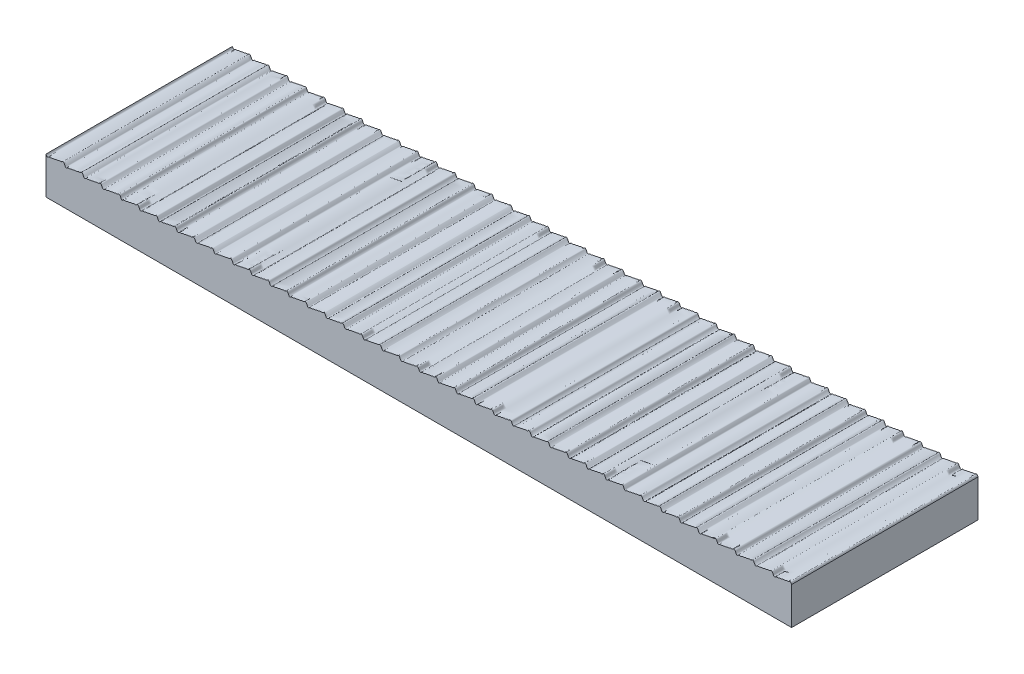
SolidWorks part; units mm, degrees
ref_plane "Ebene vorne" through (0, 0, 0) normal (0, 0, 1) x (1, 0, 0)
ref_plane "Ebene oben" through (0, 0, 0) normal (0, 1, 0) x (1, 0, 0)
ref_plane "Ebene rechts" through (0, 0, 0) normal (1, 0, 0) x (0, 0, -1)
sketch "Skizze1" plane through (0, 0, 0) normal (0, 0, 1) x (1, 0, 0)
  line L0 (0, 10) -> (200, 10) construction
  line L1 (0, 10) -> (0, 0)
  line L2 (0, 0) -> (200, 0)
  line L3 (200, 0) -> (200, 10)
  line L4 (0, 9.5082) -> (200, 9.5082) construction
  line L5 (4.9934, 10) -> (4.9934, 0) construction
  spline S0 degree 4 poles (-19.803, 9.6528) (-19.7633, 9.5821) (-19.6151, 9.4174) (-19.3083, 9.6469) (-18.9908, 9.8083) (-18.4989, 9.6674) (-18.1706, 10.0052) (-17.7456, 9.8267) (-17.4168, 10.0962) (-17.0344, 10.079) (-16.6491, 10.1079) (-16.3335, 10.3555) (-15.9223, 10.188) (-15.6947, 10.3697) (-15.3546, 10.605) (-15.1185, 10.2325) (-14.963, 9.9948) (-14.8192, 9.5069) (-14.4461, 9.4519) (-14.2053, 9.7572) (-13.9579, 9.7444) (-13.656, 9.695) (-13.3717, 9.8513) (-13.0365, 9.9455) (-12.6411, 9.8729) (-12.31, 10.1489) (-11.9067, 10.0322) (-11.5571, 10.2101) (-11.2022, 10.3278) (-10.8179, 10.1759) (-10.5875, 10.5191) (-10.221, 10.5014) (-10.0346, 10.0573) (-9.9271, 9.8175) (-9.6387, 9.3719) (-9.2968, 9.6505) (-9.0685, 9.7929) (-8.7097, 9.676) (-8.4152, 9.8172) (-8.0962, 9.9548) (-7.7194, 9.8567) (-7.3974, 10.0972) (-7.0094, 10.0787) (-6.666, 10.1116) (-6.3795, 10.3091) (-6.0887, 10.2505) (-5.8139, 10.2478) (-5.627, 10.4528) (-5.2947, 10.5743) (-5.1177, 10.1961) (-4.9533, 9.9723) (-4.8428, 9.5825) (-4.468, 9.3918) (-4.1894, 9.8304) (-3.8094, 9.6774) (-3.4534, 9.7783) (-3.1195, 9.9682) (-2.7152, 9.8504) (-2.3874, 10.1052) (-1.9985, 10.073) (-1.6253, 10.1237) (-1.2964, 10.3674) (-0.8741, 10.1443) (-0.6056, 10.5183) (-0.2367, 10.5344) (-0.0482, 10.0749) (0.0482, 9.9252) (0.2364, 9.4662) (0.6049, 9.4811) (0.8731, 9.8552) (1.2945, 9.6334) (1.6236, 9.8742) (1.9959, 9.9283) (2.385, 9.8932) (2.7127, 10.1491) (3.1165, 10.0325) (3.4516, 10.2192) (3.8061, 10.3242) (4.1879, 10.1684) (4.4643, 10.6052) (4.8406, 10.4228) (4.9511, 10.0301) (5.1166, 9.8096) (5.2897, 9.4282) (5.6231, 9.5427) (5.8097, 9.7499) (6.0823, 9.7511) (6.373, 9.69) (6.6597, 9.8829) (7.0007, 9.9251) (7.3905, 9.8977) (7.7113, 10.1421) (8.0887, 10.0464) (8.4078, 10.1778) (8.705, 10.3235) (9.0577, 10.2114) (9.2982, 10.3384) (9.6222, 10.6364) (9.9472, 10.1763) (10.0043, 9.9348) (10.3691, 9.2604) (10.7907, 9.8096) (11.1588, 9.6993) (11.5649, 9.7656) (11.8825, 9.9788) (12.3038, 9.8432) (12.6258, 10.123) (13.0238, 10.058) (13.3599, 10.1408) (13.6431, 10.3007) (13.9466, 10.264) (14.1941, 10.2296) (14.4411, 10.5519) (14.8005, 10.4852) (14.9807, 10.0519) (15.1092, 9.6777) (15.5171, 9.3158) (15.8715, 9.9263) (16.2937, 9.602) (16.6478, 9.9021) (17.0062, 9.9179) (17.4068, 9.8945) (17.7227, 10.1765) (18.1563, 9.9844) (18.478, 10.3403) (18.9832, 10.1656) (19.3029, 10.404) (19.7596, 10.6093) (19.9338, 10.0576) (20.0773, 9.9118) (20.2286, 9.4635) (20.6157, 9.4882) (20.8734, 9.865) (21.3166, 9.6243) (21.6399, 9.8962) (22.0217, 9.9148) (22.3981, 9.9098) (22.7233, 10.1394) (23.1099, 10.0479) (23.432, 10.1872) (23.7798, 10.3558) (24.1607, 10.1276) (24.4783, 10.6575) (24.9052, 10.323) (25.0095, 9.9616) (25.2229, 9.4605) (25.6053, 9.4939) (25.8395, 9.7871) (26.1068, 9.7246) (26.394, 9.7046) (26.679, 9.894) (27.0237, 9.9166) (27.4076, 9.9107) (27.7315, 10.1419) (28.0927, 10.049) (28.4104, 10.1738) (28.6792, 10.3247) (29.0482, 10.2022) (29.2939, 10.3541) (29.6654, 10.6443) (29.9601, 10.1152) (30.0326, 9.8801) (30.3897, 9.2817) (30.7591, 9.7596) (31.074, 9.7503) (31.4215, 9.6888) (31.6959, 9.9172) (32.0529, 9.9017) (32.4103, 9.9233) (32.7535, 10.1465) (33.1312, 10.0403) (33.4513, 10.2067) (33.7368, 10.3214) (34.089, 10.1903) (34.3186, 10.4154) (34.7206, 10.6199) (34.9588, 10.0597) (35.0702, 9.857) (35.3226, 9.3874) (35.6775, 9.6043) (35.8761, 9.7893) (36.2256, 9.7021) (36.505, 9.7521) (36.8106, 9.9555) (37.167, 9.8627) (37.509, 10.0134) (37.8671, 10.1257) (38.241, 10.0558) (38.5368, 10.2724) (38.8425, 10.2953) (39.1535, 10.1905) (39.3923, 10.5258) (39.7742, 10.5217) (39.9834, 10.0465) (40.0808, 9.7305) (40.4733, 9.3278) (40.8008, 9.8251) (41.142, 9.6956) (41.5075, 9.7428) (41.8041, 9.9565) (42.1834, 9.8659) (42.5219, 10.0148) (42.8675, 10.1353) (43.2803, 10.0324) (43.5862, 10.3748) (44.0585, 10.1517) (44.3243, 10.4122) (44.6996, 10.5972) (44.9012, 10.1587) (45.0431, 9.9937) (45.1786, 9.4702) (45.6383, 9.4829) (45.9468, 9.8912) (46.4361, 9.6052) (46.7557, 9.9991) (47.1705, 9.839) (47.5156, 10.0285) (47.865, 10.1178) (48.2624, 10.0565) (48.5549, 10.3089) (48.9537, 10.2577) (49.2388, 10.2431) (49.5572, 10.6429) (49.8639, 10.2998) (50.0163, 10.028) (50.1599, 9.5235) (50.5828, 9.431) (50.879, 9.8739) (51.2911, 9.6211) (51.6202, 9.8789) (51.9893, 9.9252) (52.3819, 9.8934) (52.7083, 10.1473) (53.1224, 10.0351) (53.4499, 10.2175) (53.8314, 10.3342) (54.1887, 10.1504) (54.5154, 10.6667) (54.9014, 10.2973) (55.0134, 9.9778) (55.2043, 9.485) (55.579, 9.47) (55.8205, 9.7765) (56.0758, 9.7328) (56.3726, 9.6995) (56.6543, 9.8752) (56.9969, 9.9296) (57.3834, 9.8934) (57.7068, 10.138) (58.064, 10.054) (58.3876, 10.1552) (58.6508, 10.3223) (59.0194, 10.2133) (59.2726, 10.321) (59.6462, 10.6578) (59.9699, 10.1251) (60.029, 9.8509) (60.4185, 9.2763) (60.7804, 9.7952) (61.0889, 9.7248) (61.4195, 9.7073) (61.6845, 9.8976) (62.0309, 9.9161) (62.3875, 9.9037) (62.7295, 10.1464) (63.1031, 10.0421) (63.4308, 10.1893) (63.7076, 10.3218) (64.0646, 10.2006) (64.2956, 10.3744) (64.6968, 10.6451) (64.9488, 10.0846) (65.0643, 9.8844) (65.2915, 9.4113) (65.6525, 9.5625) (65.854, 9.7942) (66.1985, 9.7056) (66.4858, 9.7398) (66.7863, 9.9486) (67.1425, 9.8709) (67.4872, 9.9912) (67.8421, 10.1353) (68.2148, 10.0469) (68.5165, 10.2596) (68.8103, 10.3009) (69.1323, 10.1915) (69.3642, 10.4848) (69.7538, 10.5629) (69.9766, 10.0518) (70.0706, 9.7769) (70.443, 9.3154) (70.7826, 9.8017) (71.1126, 9.7163) (71.4889, 9.7217) (71.7802, 9.955) (72.1586, 9.8703) (72.5013, 9.9952) (72.8418, 10.1441) (73.2582, 10.0223) (73.5643, 10.3628) (74.0302, 10.1711) (74.3081, 10.3719) (74.672, 10.6166) (74.9042, 10.168) (75.0375, 9.9958) (75.1925, 9.4432) (75.6513, 9.5107) (75.9556, 9.8714) (76.4209, 9.6117) (76.735, 9.9844) (77.145, 9.851) (77.4961, 10.0061) (77.8408, 10.127) (78.2394, 10.0482) (78.5375, 10.2951) (78.9239, 10.2736) (79.2249, 10.2214) (79.5356, 10.6435) (79.8786, 10.3083) (80.0115, 9.9997) (80.182, 9.4858) (80.5938, 9.469) (80.8547, 9.8114) (81.1646, 9.7036) (81.479, 9.7324) (81.7709, 9.9507) (82.1489, 9.8661) (82.507, 10.0043) (82.8446, 10.1266) (83.2237, 10.0572) (83.5041, 10.2525) (83.8455, 10.3145) (84.186, 10.1562) (84.5085, 10.6721) (84.8881, 10.3125) (85.0181, 9.9636) (85.1931, 9.5149) (85.5563, 9.4472) (85.8044, 9.7682) (86.0503, 9.7371) (86.3539, 9.6991) (86.6365, 9.8561) (86.9717, 9.9438) (87.37, 9.875) (87.6921, 10.155) (88.1127, 10.0234) (88.4322, 10.2287) (88.8369, 10.3063) (89.2056, 10.1833) (89.6234, 10.7392) (89.9962, 10.0739) (90.0487, 9.8298) (90.3736, 9.3651) (90.6994, 9.6572) (90.9388, 9.79) (91.2918, 9.6765) (91.5895, 9.8199) (91.9081, 9.9543) (92.2858, 9.8572) (92.607, 10.1007) (92.9962, 10.0761) (93.3385, 10.1153) (93.6253, 10.31) (93.9175, 10.2491) (94.1907, 10.2496) (94.3781, 10.4591) (94.711, 10.5696) (94.8825, 10.1922) (95.0482, 9.9706) (95.1569, 9.5835) (95.5317, 9.3914) (95.8099, 9.8311) (96.1918, 9.6767) (96.5479, 9.7798) (96.8827, 9.9678) (97.2862, 9.8508) (97.615, 10.1061) (98.0018, 10.0725) (98.3779, 10.1244) (98.7017, 10.3685) (99.1362, 10.1408) (99.3853, 10.5288) (99.7865, 10.522) (99.9157, 10.0833) (100.0843, 9.9167) (100.2135, 9.478) (100.6147, 9.4712) (100.8638, 9.8592) (101.2983, 9.6315) (101.6221, 9.8756) (101.9982, 9.9275) (102.385, 9.8939) (102.7138, 10.1492) (103.1173, 10.0322) (103.4521, 10.2202) (103.8082, 10.3233) (104.1901, 10.1689) (104.4683, 10.6086) (104.8431, 10.4165) (104.9518, 10.0294) (105.1175, 9.8078) (105.289, 9.4304) (105.6219, 9.5409) (105.8093, 9.7504) (106.0825, 9.7509) (106.3747, 9.69) (106.6615, 9.8847) (107.0038, 9.9239) (107.393, 9.8993) (107.7142, 10.1428) (108.0919, 10.0457) (108.4105, 10.1801) (108.7082, 10.3235) (109.0612, 10.21) (109.3006, 10.3428) (109.6264, 10.6349) (109.9513, 10.1702) (110.0038, 9.9261) (110.3766, 9.2608) (110.7944, 9.8167) (111.1631, 9.6937) (111.5678, 9.7713) (111.8873, 9.9766) (112.3079, 9.845) (112.63, 10.125) (113.0283, 10.0562) (113.3635, 10.1439) (113.6461, 10.3009) (113.9497, 10.2629) (114.1956, 10.2318) (114.4437, 10.5528) (114.8069, 10.4851) (114.9819, 10.0364) (115.1119, 9.6875) (115.4915, 9.3279) (115.814, 9.8438) (116.1545, 9.6855) (116.4959, 9.7475) (116.7763, 9.9428) (117.1554, 9.8734) (117.493, 9.9957) (117.8511, 10.1339) (118.2291, 10.0493) (118.521, 10.2676) (118.8354, 10.2964) (119.1453, 10.1886) (119.4062, 10.531) (119.818, 10.5142) (119.9885, 10.0003) (120.1214, 9.6917) (120.4644, 9.3565) (120.7751, 9.7786) (121.0761, 9.7264) (121.4625, 9.7049) (121.7606, 9.9518) (122.1592, 9.873) (122.5039, 9.9939) (122.855, 10.149) (123.265, 10.0156) (123.5791, 10.3883) (124.0444, 10.1286) (124.3487, 10.4893) (124.8075, 10.5568) (124.9625, 10.0042) (125.0958, 9.832) (125.328, 9.3834) (125.6919, 9.6281) (125.9698, 9.8289) (126.4357, 9.6372) (126.7418, 9.9777) (127.1582, 9.8559) (127.4987, 10.0048) (127.8414, 10.1297) (128.2198, 10.045) (128.5111, 10.2783) (128.8874, 10.2837) (129.2174, 10.1983) (129.557, 10.6846) (129.9294, 10.2231) (130.0234, 9.9482) (130.2462, 9.4371) (130.6358, 9.5152) (130.8677, 9.8085) (131.1897, 9.6991) (131.4835, 9.7404) (131.7852, 9.9531) (132.1579, 9.8647) (132.5128, 10.0088) (132.8575, 10.1291) (133.2137, 10.0514) (133.5142, 10.2602) (133.8015, 10.2944) (134.146, 10.2058) (134.3475, 10.4375) (134.7085, 10.5887) (134.9357, 10.1156) (135.0512, 9.9154) (135.3032, 9.3549) (135.7044, 9.6256) (135.9354, 9.7994) (136.2924, 9.6782) (136.5692, 9.8107) (136.8969, 9.9579) (137.2705, 9.8536) (137.6125, 10.0963) (137.9691, 10.0839) (138.3155, 10.1024) (138.5805, 10.2927) (138.9111, 10.2752) (139.2196, 10.2048) (139.5815, 10.7237) (139.971, 10.1491) (140.0301, 9.8749) (140.3538, 9.3422) (140.7274, 9.679) (140.9806, 9.7867) (141.3492, 9.6777) (141.6124, 9.8448) (141.936, 9.946) (142.2932, 9.862) (142.6166, 10.1066) (143.0031, 10.0704) (143.3457, 10.1248) (143.6274, 10.3005) (143.9242, 10.2672) (144.1795, 10.2235) (144.421, 10.53) (144.7957, 10.515) (144.9866, 10.0222) (145.0986, 9.7027) (145.4846, 9.3333) (145.8113, 9.8496) (146.1686, 9.6658) (146.5501, 9.7825) (146.8776, 9.9649) (147.2917, 9.8527) (147.6181, 10.1066) (148.0107, 10.0748) (148.3798, 10.1211) (148.7089, 10.3789) (149.121, 10.1261) (149.4172, 10.569) (149.8401, 10.4765) (149.9837, 9.972) (150.1361, 9.7002) (150.4428, 9.3571) (150.7612, 9.7569) (151.0463, 9.7423) (151.4451, 9.6911) (151.7376, 9.9435) (152.135, 9.8822) (152.4844, 9.9715) (152.8295, 10.161) (153.2443, 10.0009) (153.5639, 10.3948) (154.0532, 10.1088) (154.3617, 10.5171) (154.8214, 10.5298) (154.9569, 10.0063) (155.0988, 9.8413) (155.3004, 9.4028) (155.6757, 9.5878) (155.9415, 9.8483) (156.4138, 9.6252) (156.7197, 9.9676) (157.1325, 9.8647) (157.4781, 9.9852) (157.8166, 10.1341) (158.1959, 10.0435) (158.4925, 10.2572) (158.858, 10.3044) (159.1992, 10.1749) (159.5267, 10.6722) (159.9192, 10.2695) (160.0166, 9.9535) (160.2258, 9.4783) (160.6077, 9.4742) (160.8465, 9.8095) (161.1575, 9.7047) (161.4632, 9.7276) (161.759, 9.9442) (162.1329, 9.8743) (162.491, 9.9866) (162.833, 10.1373) (163.1894, 10.0445) (163.495, 10.2479) (163.7744, 10.2979) (164.1239, 10.2107) (164.3225, 10.3957) (164.6774, 10.6126) (164.9298, 10.143) (165.0412, 9.9403) (165.2794, 9.3801) (165.6814, 9.5846) (165.911, 9.8097) (166.2632, 9.6786) (166.5487, 9.7933) (166.8688, 9.9597) (167.2465, 9.8535) (167.5897, 10.0767) (167.9471, 10.0983) (168.3041, 10.0828) (168.5785, 10.3112) (168.926, 10.2497) (169.2409, 10.2404) (169.6103, 10.7183) (169.9674, 10.1199) (170.0399, 9.8848) (170.3346, 9.3557) (170.7061, 9.6459) (170.9518, 9.7978) (171.3208, 9.6753) (171.5896, 9.8262) (171.9073, 9.951) (172.2685, 9.8581) (172.5924, 10.0893) (172.9763, 10.0834) (173.321, 10.106) (173.606, 10.2954) (173.8932, 10.2754) (174.1605, 10.2129) (174.3947, 10.5061) (174.7771, 10.5395) (174.9905, 10.0384) (175.0948, 9.677) (175.5217, 9.3425) (175.8393, 9.8724) (176.2202, 9.6442) (176.568, 9.8128) (176.8901, 9.9521) (177.2767, 9.8606) (177.6019, 10.0902) (177.9783, 10.0852) (178.3601, 10.1038) (178.6834, 10.3757) (179.1266, 10.135) (179.3843, 10.5118) (179.7714, 10.5365) (179.9227, 10.0882) (180.0662, 9.9424) (180.2404, 9.3907) (180.6971, 9.596) (181.0168, 9.8344) (181.522, 9.6597) (181.8437, 10.0156) (182.2773, 9.8235) (182.5932, 10.1055) (182.9938, 10.0821) (183.3522, 10.0979) (183.7063, 10.398) (184.1285, 10.0737) (184.4829, 10.6842) (184.8908, 10.3223) (185.0193, 9.9481) (185.1995, 9.5148) (185.5589, 9.4481) (185.8059, 9.7704) (186.0534, 9.736) (186.3569, 9.6993) (186.6401, 9.8592) (186.9762, 9.942) (187.3742, 9.877) (187.6962, 10.1568) (188.1175, 10.0212) (188.4351, 10.2344) (188.8412, 10.3007) (189.2093, 10.1904) (189.6309, 10.7396) (189.9957, 10.0652) (190.0528, 9.8237) (190.3778, 9.3636) (190.7018, 9.6616) (190.9423, 9.7886) (191.295, 9.6765) (191.5922, 9.8222) (191.9113, 9.9536) (192.2887, 9.8579) (192.6095, 10.1023) (192.9993, 10.0749) (193.3403, 10.1171) (193.627, 10.31) (193.9177, 10.2489) (194.1903, 10.2501) (194.3769, 10.4573) (194.7103, 10.5718) (194.8834, 10.1904) (195.0489, 9.9699) (195.1594, 9.5772) (195.5357, 9.3948) (195.8121, 9.8316) (196.1939, 9.6758) (196.5484, 9.7808) (196.8835, 9.9675) (197.2873, 9.8509) (197.615, 10.1068) (198.0041, 10.0717) (198.3764, 10.1258) (198.7055, 10.3666) (199.1269, 10.1448) (199.3951, 10.5189) (199.7636, 10.5338) (199.9518, 10.0748) (200.0482, 9.9251) (200.2367, 9.4656) (200.6056, 9.4817) (200.8741, 9.8557) (201.2964, 9.6326) (201.6253, 9.8763) (201.9985, 9.927) (202.3874, 9.8948) (202.7152, 10.1496) (203.1195, 10.0318) (203.4534, 10.2217) (203.8094, 10.3226) (204.1894, 10.1696) (204.468, 10.6082) (204.8428, 10.4175) (204.9533, 10.0277) (205.1177, 9.8039) (205.2947, 9.4257) (205.627, 9.5472) (205.8139, 9.7522) (206.0887, 9.7495) (206.3795, 9.6909) (206.666, 9.8884) (207.0094, 9.9213) (207.3974, 9.9028) (207.7194, 10.1433) (208.0962, 10.0452) (208.4152, 10.1828) (208.7097, 10.324) (209.0685, 10.2071) (209.2968, 10.3495) (209.6387, 10.6281) (209.9271, 10.1825) (210.0346, 9.9427) (210.221, 9.4986) (210.5875, 9.4809) (210.8179, 9.8241) (211.2022, 9.6722) (211.5571, 9.7899) (211.9067, 9.9678) (212.31, 9.8511) (212.6411, 10.1271) (213.0365, 10.0545) (213.3717, 10.1487) (213.656, 10.305) (213.9579, 10.2556) (214.2053, 10.2428) (214.4461, 10.5481) (214.8192, 10.4931) (214.963, 10.0052) (215.1185, 9.7675) (215.3546, 9.395) (215.6947, 9.6303) (215.9223, 9.812) (216.3335, 9.6445) (216.6491, 9.8921) (217.0344, 9.921) (217.4168, 9.9038) (217.7456, 10.1733) (218.1706, 9.9948) (218.4989, 10.3326) (218.9908, 10.1917) (219.3083, 10.3531) (219.6151, 10.5826) (219.7633, 10.4179) (219.803, 10.3472) knots 0 0 0 0 0 0.000929 0.002702 0.004475 0.00586 0.007245 0.008629 0.010014 0.011394 0.012774 0.014154 0.015534 0.016466 0.017398 0.01888 0.020362 0.022087 0.023011 0.023935 0.02486 0.025784 0.027169 0.028554 0.029939 0.031324 0.032705 0.034087 0.035469 0.036851 0.03779 0.038729 0.040524 0.042319 0.043313 0.044308 0.045505 0.046703 0.0479 0.049098 0.050482 0.051865 0.053249 0.054633 0.055575 0.056517 0.057459 0.0584 0.059567 0.060734 0.06208 0.063426 0.064703 0.06598 0.067339 0.068698 0.070058 0.071417 0.072802 0.074186 0.075571 0.076955 0.078298 0.079642 0.080863 0.082084 0.083304 0.084524 0.085865 0.087206 0.08859 0.089973 0.091356 0.09274 0.094099 0.095459 0.096819 0.098179 0.099455 0.100732 0.102072 0.103411 0.104583 0.105755 0.106693 0.107631 0.108569 0.109507 0.11089 0.112273 0.113656 0.115039 0.116239 0.117439 0.118639 0.119838 0.120832 0.121825 0.123625 0.125425 0.127273 0.128654 0.130036 0.131417 0.132798 0.134182 0.135566 0.13695 0.138334 0.139263 0.140192 0.14112 0.142049 0.143754 0.145254 0.146753 0.148571 0.14995 0.15133 0.152709 0.154089 0.155473 0.156857 0.158241 0.159624 0.161416 0.163208 0.164472 0.165735 0.166893 0.168052 0.169454 0.170856 0.172238 0.17362 0.175002 0.176384 0.177682 0.17898 0.180278 0.181575 0.182943 0.184311 0.186022 0.187732 0.18944 0.190366 0.191293 0.19222 0.193147 0.19453 0.195913 0.197296 0.19868 0.199821 0.200962 0.202103 0.203244 0.204479 0.205715 0.207408 0.2091 0.210911 0.212047 0.213183 0.214319 0.215455 0.216837 0.218219 0.2196 0.220982 0.222085 0.223188 0.224291 0.225394 0.226849 0.228545 0.23024 0.231235 0.232229 0.233363 0.234496 0.23563 0.236763 0.238146 0.239529 0.240912 0.242295 0.243349 0.244404 0.245458 0.246512 0.247993 0.249679 0.251364 0.252685 0.254005 0.25527 0.256535 0.257801 0.259066 0.260448 0.26183 0.263212 0.264595 0.266102 0.26761 0.268652 0.269694 0.27109 0.272487 0.274159 0.275832 0.277215 0.278599 0.279982 0.281366 0.282692 0.284018 0.285344 0.28667 0.287783 0.288897 0.290349 0.291802 0.293568 0.294854 0.296141 0.297523 0.298905 0.300287 0.301669 0.303048 0.304427 0.305807 0.307186 0.30848 0.309774 0.311384 0.312993 0.31473 0.315655 0.31658 0.317505 0.31843 0.319813 0.321196 0.32258 0.323963 0.325101 0.326239 0.327378 0.328516 0.32976 0.331004 0.33281 0.334616 0.336421 0.337501 0.338581 0.339661 0.340741 0.342122 0.343502 0.344882 0.346263 0.347365 0.348467 0.349569 0.350671 0.352154 0.353815 0.355476 0.356498 0.35752 0.358653 0.359785 0.360918 0.36205 0.363432 0.364813 0.366195 0.367577 0.368629 0.369681 0.370733 0.371785 0.373295 0.37496 0.376626 0.377962 0.379299 0.380562 0.381826 0.383089 0.384353 0.385736 0.387119 0.388502 0.389885 0.391388 0.392891 0.393946 0.395001 0.396524 0.398048 0.399589 0.40113 0.402513 0.403897 0.40528 0.406663 0.40799 0.409317 0.410644 0.41197 0.413082 0.414193 0.415775 0.417357 0.41917 0.420234 0.421299 0.422363 0.423428 0.424811 0.426194 0.427577 0.42896 0.430132 0.431304 0.432476 0.433647 0.435284 0.436789 0.438294 0.440035 0.44096 0.441886 0.442811 0.443736 0.44512 0.446503 0.447887 0.44927 0.450653 0.452036 0.453419 0.454802 0.456618 0.458433 0.460248 0.461242 0.462235 0.463435 0.464634 0.465834 0.467034 0.468418 0.469801 0.471185 0.472568 0.473511 0.474454 0.475397 0.47634 0.477502 0.478664 0.479997 0.481329 0.482616 0.483902 0.485262 0.486622 0.487982 0.489342 0.490725 0.492108 0.493491 0.494874 0.496233 0.497592 0.498796 0.5 0.501204 0.502408 0.503767 0.505126 0.506509 0.507892 0.509275 0.510658 0.512018 0.513378 0.514738 0.516098 0.517384 0.518671 0.520003 0.521336 0.522498 0.52366 0.524603 0.525546 0.526489 0.527432 0.528815 0.530199 0.531582 0.532966 0.534166 0.535366 0.536565 0.537765 0.538758 0.539752 0.541567 0.543382 0.545198 0.546581 0.547964 0.549347 0.55073 0.552113 0.553497 0.55488 0.556264 0.557189 0.558114 0.55904 0.559965 0.561706 0.563211 0.564716 0.566353 0.567524 0.568696 0.569868 0.57104 0.572423 0.573806 0.575189 0.576572 0.577637 0.578701 0.579766 0.58083 0.582643 0.584225 0.585807 0.586918 0.58803 0.589356 0.590683 0.59201 0.593337 0.59472 0.596103 0.597487 0.59887 0.600411 0.601952 0.603476 0.604999 0.606054 0.607109 0.608612 0.610115 0.611498 0.612881 0.614264 0.615647 0.616911 0.618174 0.619438 0.620701 0.622038 0.623374 0.62504 0.626705 0.628215 0.629267 0.630319 0.631371 0.632423 0.633805 0.635187 0.636568 0.63795 0.639082 0.640215 0.641347 0.64248 0.643502 0.644524 0.646185 0.647846 0.649329 0.650431 0.651533 0.652635 0.653737 0.655118 0.656498 0.657878 0.659259 0.660339 0.661419 0.662499 0.663579 0.665384 0.66719 0.668996 0.67024 0.671484 0.672622 0.673761 0.674899 0.676037 0.67742 0.678804 0.680187 0.68157 0.682495 0.68342 0.684345 0.68527 0.687007 0.688616 0.690226 0.69152 0.692814 0.694193 0.695573 0.696952 0.698331 0.699713 0.701095 0.702477 0.703859 0.705146 0.706432 0.708198 0.709651 0.711103 0.712217 0.71333 0.714656 0.715982 0.717308 0.718634 0.720018 0.721401 0.722785 0.724168 0.725841 0.727513 0.72891 0.730306 0.731348 0.73239 0.733898 0.735405 0.736788 0.73817 0.739552 0.740934 0.742199 0.743465 0.74473 0.745995 0.747315 0.748636 0.750321 0.752007 0.753488 0.754542 0.755596 0.756651 0.757705 0.759088 0.760471 0.761854 0.763237 0.76437 0.765504 0.766637 0.767771 0.768765 0.76976 0.771455 0.773151 0.774606 0.775709 0.776812 0.777915 0.779018 0.7804 0.781781 0.783163 0.784545 0.785681 0.786817 0.787953 0.789089 0.7909 0.792592 0.794285 0.795521 0.796756 0.797897 0.799038 0.800179 0.80132 0.802704 0.804087 0.80547 0.806853 0.80778 0.808707 0.809634 0.81056 0.812268 0.813978 0.815689 0.817057 0.818425 0.819722 0.82102 0.822318 0.823616 0.824998 0.82638 0.827762 0.829144 0.830546 0.831948 0.833107 0.834265 0.835528 0.836792 0.838584 0.840376 0.841759 0.843143 0.844527 0.845911 0.847291 0.84867 0.85005 0.851429 0.853247 0.854746 0.856246 0.857951 0.85888 0.859808 0.860737 0.861666 0.86305 0.864434 0.865818 0.867202 0.868583 0.869964 0.871346 0.872727 0.874575 0.876375 0.878175 0.879168 0.880162 0.881361 0.882561 0.883761 0.884961 0.886344 0.887727 0.88911 0.890493 0.891431 0.892369 0.893307 0.894245 0.895417 0.896589 0.897928 0.899268 0.900545 0.901821 0.903181 0.904541 0.905901 0.90726 0.908644 0.910027 0.91141 0.912794 0.914135 0.915476 0.916696 0.917916 0.919137 0.920358 0.921702 0.923045 0.924429 0.925814 0.927198 0.928583 0.929942 0.931302 0.932661 0.93402 0.935297 0.936574 0.93792 0.939266 0.940433 0.9416 0.942541 0.943483 0.944425 0.945367 0.946751 0.948135 0.949518 0.950902 0.9521 0.953297 0.954495 0.955692 0.956687 0.957681 0.959476 0.961271 0.96221 0.963149 0.964531 0.965913 0.967295 0.968676 0.970061 0.971446 0.972831 0.974216 0.97514 0.976065 0.976989 0.977913 0.979638 0.98112 0.982602 0.983534 0.984466 0.985846 0.987226 0.988606 0.989986 0.991371 0.992755 0.99414 0.995525 0.997298 0.999071 1 1 1 1 1 construction
  spline S1 degree 4 poles (0, 10) (0.0314, 9.9377) (0.0941, 9.8132) (0.2364, 9.4662) (0.6049, 9.4811) (0.8731, 9.8552) (1.2945, 9.6334) (1.6236, 9.8742) (1.9959, 9.9283) (2.385, 9.8932) (2.7127, 10.1491) (3.1165, 10.0325) (3.4516, 10.2192) (3.8061, 10.3242) (4.1879, 10.1684) (4.4643, 10.6052) (4.8406, 10.4228) (4.9511, 10.0301) (5.1166, 9.8096) (5.2897, 9.4282) (5.6231, 9.5427) (5.8097, 9.7499) (6.0823, 9.7511) (6.373, 9.69) (6.6597, 9.8829) (7.0007, 9.9251) (7.3905, 9.8977) (7.7113, 10.1421) (8.0887, 10.0464) (8.4078, 10.1778) (8.705, 10.3235) (9.0577, 10.2114) (9.2982, 10.3384) (9.6222, 10.6364) (9.9472, 10.1763) (10.0043, 9.9348) (10.3691, 9.2604) (10.7907, 9.8096) (11.1588, 9.6993) (11.5649, 9.7656) (11.8825, 9.9788) (12.3038, 9.8432) (12.6258, 10.123) (13.0238, 10.058) (13.3599, 10.1408) (13.6431, 10.3007) (13.9466, 10.264) (14.1941, 10.2296) (14.4411, 10.5519) (14.8005, 10.4852) (14.9807, 10.0519) (15.1092, 9.6777) (15.5171, 9.3158) (15.8715, 9.9263) (16.2937, 9.602) (16.6478, 9.9021) (17.0062, 9.9179) (17.4068, 9.8945) (17.7227, 10.1765) (18.1563, 9.9844) (18.478, 10.3403) (18.9832, 10.1656) (19.3029, 10.404) (19.7596, 10.6093) (19.9338, 10.0576) (20.0773, 9.9118) (20.2286, 9.4635) (20.6157, 9.4882) (20.8734, 9.865) (21.3166, 9.6243) (21.6399, 9.8962) (22.0217, 9.9148) (22.3981, 9.9098) (22.7233, 10.1394) (23.1099, 10.0479) (23.432, 10.1872) (23.7798, 10.3558) (24.1607, 10.1276) (24.4783, 10.6575) (24.9052, 10.323) (25.0095, 9.9616) (25.2229, 9.4605) (25.6053, 9.4939) (25.8395, 9.7871) (26.1068, 9.7246) (26.394, 9.7046) (26.679, 9.894) (27.0237, 9.9166) (27.4076, 9.9107) (27.7315, 10.1419) (28.0927, 10.049) (28.4104, 10.1738) (28.6792, 10.3247) (29.0482, 10.2022) (29.2939, 10.3541) (29.6654, 10.6443) (29.9601, 10.1152) (30.0326, 9.8801) (30.3897, 9.2817) (30.7591, 9.7596) (31.074, 9.7503) (31.4215, 9.6888) (31.6959, 9.9172) (32.0529, 9.9017) (32.4103, 9.9233) (32.7535, 10.1465) (33.1312, 10.0403) (33.4513, 10.2067) (33.7368, 10.3214) (34.089, 10.1903) (34.3186, 10.4154) (34.7206, 10.6199) (34.9588, 10.0597) (35.0702, 9.857) (35.3226, 9.3874) (35.6775, 9.6043) (35.8761, 9.7893) (36.2256, 9.7021) (36.505, 9.7521) (36.8106, 9.9555) (37.167, 9.8627) (37.509, 10.0134) (37.8671, 10.1257) (38.241, 10.0558) (38.5368, 10.2724) (38.8425, 10.2953) (39.1535, 10.1905) (39.3923, 10.5258) (39.7742, 10.5217) (39.9834, 10.0465) (40.0808, 9.7305) (40.4733, 9.3278) (40.8008, 9.8251) (41.142, 9.6956) (41.5075, 9.7428) (41.8041, 9.9565) (42.1834, 9.8659) (42.5219, 10.0148) (42.8675, 10.1353) (43.2803, 10.0324) (43.5862, 10.3748) (44.0585, 10.1517) (44.3243, 10.4122) (44.6996, 10.5972) (44.9012, 10.1587) (45.0431, 9.9937) (45.1786, 9.4702) (45.6383, 9.4829) (45.9468, 9.8912) (46.4361, 9.6052) (46.7557, 9.9991) (47.1705, 9.839) (47.5156, 10.0285) (47.865, 10.1178) (48.2624, 10.0565) (48.5549, 10.3089) (48.9537, 10.2577) (49.2388, 10.2431) (49.5572, 10.6429) (49.8639, 10.2998) (50.0163, 10.028) (50.1599, 9.5235) (50.5828, 9.431) (50.879, 9.8739) (51.2911, 9.6211) (51.6202, 9.8789) (51.9893, 9.9252) (52.3819, 9.8934) (52.7083, 10.1473) (53.1224, 10.0351) (53.4499, 10.2175) (53.8314, 10.3342) (54.1887, 10.1504) (54.5154, 10.6667) (54.9014, 10.2973) (55.0134, 9.9778) (55.2043, 9.485) (55.579, 9.47) (55.8205, 9.7765) (56.0758, 9.7328) (56.3726, 9.6995) (56.6543, 9.8752) (56.9969, 9.9296) (57.3834, 9.8934) (57.7068, 10.138) (58.064, 10.054) (58.3876, 10.1552) (58.6508, 10.3223) (59.0194, 10.2133) (59.2726, 10.321) (59.6462, 10.6578) (59.9699, 10.1251) (60.029, 9.8509) (60.4185, 9.2763) (60.7804, 9.7952) (61.0889, 9.7248) (61.4195, 9.7073) (61.6845, 9.8976) (62.0309, 9.9161) (62.3875, 9.9037) (62.7295, 10.1464) (63.1031, 10.0421) (63.4308, 10.1893) (63.7076, 10.3218) (64.0646, 10.2006) (64.2956, 10.3744) (64.6968, 10.6451) (64.9488, 10.0846) (65.0643, 9.8844) (65.2915, 9.4113) (65.6525, 9.5625) (65.854, 9.7942) (66.1985, 9.7056) (66.4858, 9.7398) (66.7863, 9.9486) (67.1425, 9.8709) (67.4872, 9.9912) (67.8421, 10.1353) (68.2148, 10.0469) (68.5165, 10.2596) (68.8103, 10.3009) (69.1323, 10.1915) (69.3642, 10.4848) (69.7538, 10.5629) (69.9766, 10.0518) (70.0706, 9.7769) (70.443, 9.3154) (70.7826, 9.8017) (71.1126, 9.7163) (71.4889, 9.7217) (71.7802, 9.955) (72.1586, 9.8703) (72.5013, 9.9952) (72.8418, 10.1441) (73.2582, 10.0223) (73.5643, 10.3628) (74.0302, 10.1711) (74.3081, 10.3719) (74.672, 10.6166) (74.9042, 10.168) (75.0375, 9.9958) (75.1925, 9.4432) (75.6513, 9.5107) (75.9556, 9.8714) (76.4209, 9.6117) (76.735, 9.9844) (77.145, 9.851) (77.4961, 10.0061) (77.8408, 10.127) (78.2394, 10.0482) (78.5375, 10.2951) (78.9239, 10.2736) (79.2249, 10.2214) (79.5356, 10.6435) (79.8786, 10.3083) (80.0115, 9.9997) (80.182, 9.4858) (80.5938, 9.469) (80.8547, 9.8114) (81.1646, 9.7036) (81.479, 9.7324) (81.7709, 9.9507) (82.1489, 9.8661) (82.507, 10.0043) (82.8446, 10.1266) (83.2237, 10.0572) (83.5041, 10.2525) (83.8455, 10.3145) (84.186, 10.1562) (84.5085, 10.6721) (84.8881, 10.3125) (85.0181, 9.9636) (85.1931, 9.5149) (85.5563, 9.4472) (85.8044, 9.7682) (86.0503, 9.7371) (86.3539, 9.6991) (86.6365, 9.8561) (86.9717, 9.9438) (87.37, 9.875) (87.6921, 10.155) (88.1127, 10.0234) (88.4322, 10.2287) (88.8369, 10.3063) (89.2056, 10.1833) (89.6234, 10.7392) (89.9962, 10.0739) (90.0487, 9.8298) (90.3736, 9.3651) (90.6994, 9.6572) (90.9388, 9.79) (91.2918, 9.6765) (91.5895, 9.8199) (91.9081, 9.9543) (92.2858, 9.8572) (92.607, 10.1007) (92.9962, 10.0761) (93.3385, 10.1153) (93.6253, 10.31) (93.9175, 10.2491) (94.1907, 10.2496) (94.3781, 10.4591) (94.711, 10.5696) (94.8825, 10.1922) (95.0482, 9.9706) (95.1569, 9.5835) (95.5317, 9.3914) (95.8099, 9.8311) (96.1918, 9.6767) (96.5479, 9.7798) (96.8827, 9.9678) (97.2862, 9.8508) (97.615, 10.1061) (98.0018, 10.0725) (98.3779, 10.1244) (98.7017, 10.3685) (99.1362, 10.1408) (99.3853, 10.5288) (99.7865, 10.522) (99.9157, 10.0833) (100.0843, 9.9167) (100.2135, 9.478) (100.6147, 9.4712) (100.8638, 9.8592) (101.2983, 9.6315) (101.6221, 9.8756) (101.9982, 9.9275) (102.385, 9.8939) (102.7138, 10.1492) (103.1173, 10.0322) (103.4521, 10.2202) (103.8082, 10.3233) (104.1901, 10.1689) (104.4683, 10.6086) (104.8431, 10.4165) (104.9518, 10.0294) (105.1175, 9.8078) (105.289, 9.4304) (105.6219, 9.5409) (105.8093, 9.7504) (106.0825, 9.7509) (106.3747, 9.69) (106.6615, 9.8847) (107.0038, 9.9239) (107.393, 9.8993) (107.7142, 10.1428) (108.0919, 10.0457) (108.4105, 10.1801) (108.7082, 10.3235) (109.0612, 10.21) (109.3006, 10.3428) (109.6264, 10.6349) (109.9513, 10.1702) (110.0038, 9.9261) (110.3766, 9.2608) (110.7944, 9.8167) (111.1631, 9.6937) (111.5678, 9.7713) (111.8873, 9.9766) (112.3079, 9.845) (112.63, 10.125) (113.0283, 10.0562) (113.3635, 10.1439) (113.6461, 10.3009) (113.9497, 10.2629) (114.1956, 10.2318) (114.4437, 10.5528) (114.8069, 10.4851) (114.9819, 10.0364) (115.1119, 9.6875) (115.4915, 9.3279) (115.814, 9.8438) (116.1545, 9.6855) (116.4959, 9.7475) (116.7763, 9.9428) (117.1554, 9.8734) (117.493, 9.9957) (117.8511, 10.1339) (118.2291, 10.0493) (118.521, 10.2676) (118.8354, 10.2964) (119.1453, 10.1886) (119.4062, 10.531) (119.818, 10.5142) (119.9885, 10.0003) (120.1214, 9.6917) (120.4644, 9.3565) (120.7751, 9.7786) (121.0761, 9.7264) (121.4625, 9.7049) (121.7606, 9.9518) (122.1592, 9.873) (122.5039, 9.9939) (122.855, 10.149) (123.265, 10.0156) (123.5791, 10.3883) (124.0444, 10.1286) (124.3487, 10.4893) (124.8075, 10.5568) (124.9625, 10.0042) (125.0958, 9.832) (125.328, 9.3834) (125.6919, 9.6281) (125.9698, 9.8289) (126.4357, 9.6372) (126.7418, 9.9777) (127.1582, 9.8559) (127.4987, 10.0048) (127.8414, 10.1297) (128.2198, 10.045) (128.5111, 10.2783) (128.8874, 10.2837) (129.2174, 10.1983) (129.557, 10.6846) (129.9294, 10.2231) (130.0234, 9.9482) (130.2462, 9.4371) (130.6358, 9.5152) (130.8677, 9.8085) (131.1897, 9.6991) (131.4835, 9.7404) (131.7852, 9.9531) (132.1579, 9.8647) (132.5128, 10.0088) (132.8575, 10.1291) (133.2137, 10.0514) (133.5142, 10.2602) (133.8015, 10.2944) (134.146, 10.2058) (134.3475, 10.4375) (134.7085, 10.5887) (134.9357, 10.1156) (135.0512, 9.9154) (135.3032, 9.3549) (135.7044, 9.6256) (135.9354, 9.7994) (136.2924, 9.6782) (136.5692, 9.8107) (136.8969, 9.9579) (137.2705, 9.8536) (137.6125, 10.0963) (137.9691, 10.0839) (138.3155, 10.1024) (138.5805, 10.2927) (138.9111, 10.2752) (139.2196, 10.2048) (139.5815, 10.7237) (139.971, 10.1491) (140.0301, 9.8749) (140.3538, 9.3422) (140.7274, 9.679) (140.9806, 9.7867) (141.3492, 9.6777) (141.6124, 9.8448) (141.936, 9.946) (142.2932, 9.862) (142.6166, 10.1066) (143.0031, 10.0704) (143.3457, 10.1248) (143.6274, 10.3005) (143.9242, 10.2672) (144.1795, 10.2235) (144.421, 10.53) (144.7957, 10.515) (144.9866, 10.0222) (145.0986, 9.7027) (145.4846, 9.3333) (145.8113, 9.8496) (146.1686, 9.6658) (146.5501, 9.7825) (146.8776, 9.9649) (147.2917, 9.8527) (147.6181, 10.1066) (148.0107, 10.0748) (148.3798, 10.1211) (148.7089, 10.3789) (149.121, 10.1261) (149.4172, 10.569) (149.8401, 10.4765) (149.9837, 9.972) (150.1361, 9.7002) (150.4428, 9.3571) (150.7612, 9.7569) (151.0463, 9.7423) (151.4451, 9.6911) (151.7376, 9.9435) (152.135, 9.8822) (152.4844, 9.9715) (152.8295, 10.161) (153.2443, 10.0009) (153.5639, 10.3948) (154.0532, 10.1088) (154.3617, 10.5171) (154.8214, 10.5298) (154.9569, 10.0063) (155.0988, 9.8413) (155.3004, 9.4028) (155.6757, 9.5878) (155.9415, 9.8483) (156.4138, 9.6252) (156.7197, 9.9676) (157.1325, 9.8647) (157.4781, 9.9852) (157.8166, 10.1341) (158.1959, 10.0435) (158.4925, 10.2572) (158.858, 10.3044) (159.1992, 10.1749) (159.5267, 10.6722) (159.9192, 10.2695) (160.0166, 9.9535) (160.2258, 9.4783) (160.6077, 9.4742) (160.8465, 9.8095) (161.1575, 9.7047) (161.4632, 9.7276) (161.759, 9.9442) (162.1329, 9.8743) (162.491, 9.9866) (162.833, 10.1373) (163.1894, 10.0445) (163.495, 10.2479) (163.7744, 10.2979) (164.1239, 10.2107) (164.3225, 10.3957) (164.6774, 10.6126) (164.9298, 10.143) (165.0412, 9.9403) (165.2794, 9.3801) (165.6814, 9.5846) (165.911, 9.8097) (166.2632, 9.6786) (166.5487, 9.7933) (166.8688, 9.9597) (167.2465, 9.8535) (167.5897, 10.0767) (167.9471, 10.0983) (168.3041, 10.0828) (168.5785, 10.3112) (168.926, 10.2497) (169.2409, 10.2404) (169.6103, 10.7183) (169.9674, 10.1199) (170.0399, 9.8848) (170.3346, 9.3557) (170.7061, 9.6459) (170.9518, 9.7978) (171.3208, 9.6753) (171.5896, 9.8262) (171.9073, 9.951) (172.2685, 9.8581) (172.5924, 10.0893) (172.9763, 10.0834) (173.321, 10.106) (173.606, 10.2954) (173.8932, 10.2754) (174.1605, 10.2129) (174.3947, 10.5061) (174.7771, 10.5395) (174.9905, 10.0384) (175.0948, 9.677) (175.5217, 9.3425) (175.8393, 9.8724) (176.2202, 9.6442) (176.568, 9.8128) (176.8901, 9.9521) (177.2767, 9.8606) (177.6019, 10.0902) (177.9783, 10.0852) (178.3601, 10.1038) (178.6834, 10.3757) (179.1266, 10.135) (179.3843, 10.5118) (179.7714, 10.5365) (179.9227, 10.0882) (180.0662, 9.9424) (180.2404, 9.3907) (180.6971, 9.596) (181.0168, 9.8344) (181.522, 9.6597) (181.8437, 10.0156) (182.2773, 9.8235) (182.5932, 10.1055) (182.9938, 10.0821) (183.3522, 10.0979) (183.7063, 10.398) (184.1285, 10.0737) (184.4829, 10.6842) (184.8908, 10.3223) (185.0193, 9.9481) (185.1995, 9.5148) (185.5589, 9.4481) (185.8059, 9.7704) (186.0534, 9.736) (186.3569, 9.6993) (186.6401, 9.8592) (186.9762, 9.942) (187.3742, 9.877) (187.6962, 10.1568) (188.1175, 10.0212) (188.4351, 10.2344) (188.8412, 10.3007) (189.2093, 10.1904) (189.6309, 10.7396) (189.9957, 10.0652) (190.0528, 9.8237) (190.3778, 9.3636) (190.7018, 9.6616) (190.9423, 9.7886) (191.295, 9.6765) (191.5922, 9.8222) (191.9113, 9.9536) (192.2887, 9.8579) (192.6095, 10.1023) (192.9993, 10.0749) (193.3403, 10.1171) (193.627, 10.31) (193.9177, 10.2489) (194.1903, 10.2501) (194.3769, 10.4573) (194.7103, 10.5718) (194.8834, 10.1904) (195.0489, 9.9699) (195.1594, 9.5772) (195.5357, 9.3948) (195.8121, 9.8316) (196.1939, 9.6758) (196.5484, 9.7808) (196.8835, 9.9675) (197.2873, 9.8509) (197.615, 10.1068) (198.0041, 10.0717) (198.3764, 10.1258) (198.7055, 10.3666) (199.1269, 10.1448) (199.3951, 10.5189) (199.7636, 10.5338) (199.9059, 10.1868) (199.9686, 10.0623) (200, 10) knots 0.082084 0.082084 0.082084 0.082084 0.082084 0.083304 0.084524 0.085865 0.087206 0.08859 0.089973 0.091356 0.09274 0.094099 0.095459 0.096819 0.098179 0.099455 0.100732 0.102072 0.103411 0.104583 0.105755 0.106693 0.107631 0.108569 0.109507 0.11089 0.112273 0.113656 0.115039 0.116239 0.117439 0.118639 0.119838 0.120832 0.121825 0.123625 0.125425 0.127273 0.128654 0.130036 0.131417 0.132798 0.134182 0.135566 0.13695 0.138334 0.139263 0.140192 0.14112 0.142049 0.143754 0.145254 0.146753 0.148571 0.14995 0.15133 0.152709 0.154089 0.155473 0.156857 0.158241 0.159624 0.161416 0.163208 0.164472 0.165735 0.166893 0.168052 0.169454 0.170856 0.172238 0.17362 0.175002 0.176384 0.177682 0.17898 0.180278 0.181575 0.182943 0.184311 0.186022 0.187732 0.18944 0.190366 0.191293 0.19222 0.193147 0.19453 0.195913 0.197296 0.19868 0.199821 0.200962 0.202103 0.203244 0.204479 0.205715 0.207408 0.2091 0.210911 0.212047 0.213183 0.214319 0.215455 0.216837 0.218219 0.2196 0.220982 0.222085 0.223188 0.224291 0.225394 0.226849 0.228545 0.23024 0.231235 0.232229 0.233363 0.234496 0.23563 0.236763 0.238146 0.239529 0.240912 0.242295 0.243349 0.244404 0.245458 0.246512 0.247993 0.249679 0.251364 0.252685 0.254005 0.25527 0.256535 0.257801 0.259066 0.260448 0.26183 0.263212 0.264595 0.266102 0.26761 0.268652 0.269694 0.27109 0.272487 0.274159 0.275832 0.277215 0.278599 0.279982 0.281366 0.282692 0.284018 0.285344 0.28667 0.287783 0.288897 0.290349 0.291802 0.293568 0.294854 0.296141 0.297523 0.298905 0.300287 0.301669 0.303048 0.304427 0.305807 0.307186 0.30848 0.309774 0.311384 0.312993 0.31473 0.315655 0.31658 0.317505 0.31843 0.319813 0.321196 0.32258 0.323963 0.325101 0.326239 0.327378 0.328516 0.32976 0.331004 0.33281 0.334616 0.336421 0.337501 0.338581 0.339661 0.340741 0.342122 0.343502 0.344882 0.346263 0.347365 0.348467 0.349569 0.350671 0.352154 0.353815 0.355476 0.356498 0.35752 0.358653 0.359785 0.360918 0.36205 0.363432 0.364813 0.366195 0.367577 0.368629 0.369681 0.370733 0.371785 0.373295 0.37496 0.376626 0.377962 0.379299 0.380562 0.381826 0.383089 0.384353 0.385736 0.387119 0.388502 0.389885 0.391388 0.392891 0.393946 0.395001 0.396524 0.398048 0.399589 0.40113 0.402513 0.403897 0.40528 0.406663 0.40799 0.409317 0.410644 0.41197 0.413082 0.414193 0.415775 0.417357 0.41917 0.420234 0.421299 0.422363 0.423428 0.424811 0.426194 0.427577 0.42896 0.430132 0.431304 0.432476 0.433647 0.435284 0.436789 0.438294 0.440035 0.44096 0.441886 0.442811 0.443736 0.44512 0.446503 0.447887 0.44927 0.450653 0.452036 0.453419 0.454802 0.456618 0.458433 0.460248 0.461242 0.462235 0.463435 0.464634 0.465834 0.467034 0.468418 0.469801 0.471185 0.472568 0.473511 0.474454 0.475397 0.47634 0.477502 0.478664 0.479997 0.481329 0.482616 0.483902 0.485262 0.486622 0.487982 0.489342 0.490725 0.492108 0.493491 0.494874 0.496233 0.497592 0.498796 0.5 0.501204 0.502408 0.503767 0.505126 0.506509 0.507892 0.509275 0.510658 0.512018 0.513378 0.514738 0.516098 0.517384 0.518671 0.520003 0.521336 0.522498 0.52366 0.524603 0.525546 0.526489 0.527432 0.528815 0.530199 0.531582 0.532966 0.534166 0.535366 0.536565 0.537765 0.538758 0.539752 0.541567 0.543382 0.545198 0.546581 0.547964 0.549347 0.55073 0.552113 0.553497 0.55488 0.556264 0.557189 0.558114 0.55904 0.559965 0.561706 0.563211 0.564716 0.566353 0.567524 0.568696 0.569868 0.57104 0.572423 0.573806 0.575189 0.576572 0.577637 0.578701 0.579766 0.58083 0.582643 0.584225 0.585807 0.586918 0.58803 0.589356 0.590683 0.59201 0.593337 0.59472 0.596103 0.597487 0.59887 0.600411 0.601952 0.603476 0.604999 0.606054 0.607109 0.608612 0.610115 0.611498 0.612881 0.614264 0.615647 0.616911 0.618174 0.619438 0.620701 0.622038 0.623374 0.62504 0.626705 0.628215 0.629267 0.630319 0.631371 0.632423 0.633805 0.635187 0.636568 0.63795 0.639082 0.640215 0.641347 0.64248 0.643502 0.644524 0.646185 0.647846 0.649329 0.650431 0.651533 0.652635 0.653737 0.655118 0.656498 0.657878 0.659259 0.660339 0.661419 0.662499 0.663579 0.665384 0.66719 0.668996 0.67024 0.671484 0.672622 0.673761 0.674899 0.676037 0.67742 0.678804 0.680187 0.68157 0.682495 0.68342 0.684345 0.68527 0.687007 0.688616 0.690226 0.69152 0.692814 0.694193 0.695573 0.696952 0.698331 0.699713 0.701095 0.702477 0.703859 0.705146 0.706432 0.708198 0.709651 0.711103 0.712217 0.71333 0.714656 0.715982 0.717308 0.718634 0.720018 0.721401 0.722785 0.724168 0.725841 0.727513 0.72891 0.730306 0.731348 0.73239 0.733898 0.735405 0.736788 0.73817 0.739552 0.740934 0.742199 0.743465 0.74473 0.745995 0.747315 0.748636 0.750321 0.752007 0.753488 0.754542 0.755596 0.756651 0.757705 0.759088 0.760471 0.761854 0.763237 0.76437 0.765504 0.766637 0.767771 0.768765 0.76976 0.771455 0.773151 0.774606 0.775709 0.776812 0.777915 0.779018 0.7804 0.781781 0.783163 0.784545 0.785681 0.786817 0.787953 0.789089 0.7909 0.792592 0.794285 0.795521 0.796756 0.797897 0.799038 0.800179 0.80132 0.802704 0.804087 0.80547 0.806853 0.80778 0.808707 0.809634 0.81056 0.812268 0.813978 0.815689 0.817057 0.818425 0.819722 0.82102 0.822318 0.823616 0.824998 0.82638 0.827762 0.829144 0.830546 0.831948 0.833107 0.834265 0.835528 0.836792 0.838584 0.840376 0.841759 0.843143 0.844527 0.845911 0.847291 0.84867 0.85005 0.851429 0.853247 0.854746 0.856246 0.857951 0.85888 0.859808 0.860737 0.861666 0.86305 0.864434 0.865818 0.867202 0.868583 0.869964 0.871346 0.872727 0.874575 0.876375 0.878175 0.879168 0.880162 0.881361 0.882561 0.883761 0.884961 0.886344 0.887727 0.88911 0.890493 0.891431 0.892369 0.893307 0.894245 0.895417 0.896589 0.897928 0.899268 0.900545 0.901821 0.903181 0.904541 0.905901 0.90726 0.908644 0.910027 0.91141 0.912794 0.914135 0.915476 0.916696 0.917916 0.917916 0.917916 0.917916 0.917916
  point P9 (4.9934, 10)
  point P10 (0, 0)
  dimension "D1" = 10
  dimension "D2" = 200
  dimension "D3" = 4.9934
  dimension "D4" = 0.4918
extrude "Aufsatz-Linear austragen1" add sketch "Skizze1" along normal blind 50
